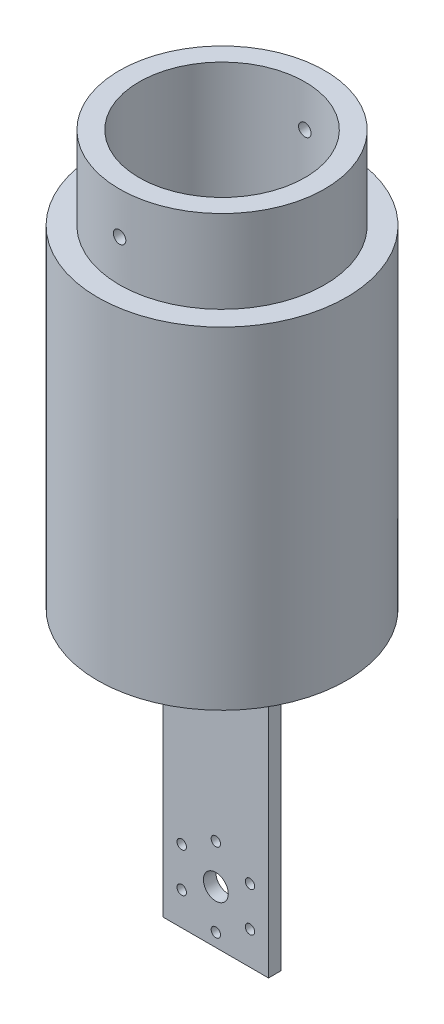
SolidWorks part; units mm, degrees
ref_plane "Front Plane" through (0, 0, 0) normal (0, 0, 1) x (1, 0, 0)
ref_plane "Top Plane" through (0, 0, 0) normal (0, 1, 0) x (1, 0, 0)
ref_plane "Right Plane" through (0, 0, 0) normal (1, 0, 0) x (0, 0, -1)
sketch "Sketch2" plane through (0, 0, 0) normal (0, 1, 0) x (1, 0, 0)
  line L0 (0, 0) -> (25.4, 0)
  line L1 (25.4, 0) -> (25.4, 3)
  line L2 (25.4, 3) -> (0, 3)
  line L3 (0, 3) -> (0, 0)
  dimension "D2" = 3
  dimension "D1" = 25.4
extrude "Boss-Extrude1" add sketch "Sketch2" along normal blind 70
sketch "Sketch3" plane through (0, 0, 0) normal (0, 0, 1) x (1, 0, 0)
  line L0 (0, 0) -> (12.7, 0) construction
  line L1 (0, 0) -> (25.4, 0) construction
  line L2 (12.7, 0) -> (12.7, 12.7) construction
  circle A0 centre (12.7, 12.7) radius 3
  circle A2 centre (12.7, 22.2) radius 1.4
  circle A3 centre (20.9272, 17.45) radius 1.4
  circle A4 centre (20.9272, 7.95) radius 1.4
  circle A5 centre (12.7, 3.2) radius 1.4
  circle A6 centre (4.4728, 7.95) radius 1.4
  circle A7 centre (4.4728, 17.45) radius 1.4
  point P23 (12.7, 12.7)
  dimension "D2" = 6
  dimension "D4" = 2.8
  dimension "D1" = 12.7
  dimension "D5" = 6
sketch "Sketch4" plane through (0, 70, 0) normal (0, 1, 0) x (1, 0, 0)
  circle A0 centre (12.7, 1.5) radius 30
  dimension "D1" = 60
extrude "Boss-Extrude2" add sketch "Sketch4" along normal blind 10
sketch "Sketch5" plane through (0, 80, 0) normal (0, 1, 0) x (1, 0, 0)
  circle A0 centre (12.7, 1.5) radius 30
  circle A1 centre (12.7, 1.5) radius 20
  dimension "D1" = 40
extrude "Boss-Extrude3" add sketch "Sketch5" along normal blind 70
sketch "Sketch8" plane through (0, 150, 0) normal (0, 1, 0) x (1, 0, 0)
  circle A0 centre (12.7, 1.5) radius 24.75
  circle A1 centre (12.7, 1.5) radius 20
  dimension "D1" = 49.5
extrude "Boss-Extrude4" add sketch "Sketch8" along normal blind 20
sketch "Sketch9" plane through (0, 0, 0) normal (0, 0, 1) x (1, 0, 0)
  line L0 (12.7, 170) -> (12.7, 160) construction
  line L1 (37.45, 170) -> (-12.05, 170) construction
  circle A0 centre (12.7, 160) radius 1.5
  dimension "D2" = 3
  dimension "D1" = 10
extrude "Cut-Extrude4" cut sketch "Sketch9" against normal through all and the other way through all
hole_wizard "#4-40 Tapped Hole1" positions "Sketch11" profile "Sketch10" tap size "#4-40" standard "ANSI Inch"
sketch "Sketch11" plane through (0, 0, 0) normal (0, 0, 1) x (1, 0, 0)
  point P0 (12.7, 22.2)
  point P3 (20.9272, 17.45)
  point P6 (20.9272, 7.95)
  point P9 (12.7, 3.2)
  point P12 (4.4728, 7.95)
  point P15 (4.4728, 17.45)
sketch "Sketch10" plane through (12.7, 22.2, 0) normal (1, 0, 0) x (0, -1, 0)
  line L0 (0, 0) -> (0, 8.2792)
  line L1 (0, 8.2792) -> (1.1303, 7.6)
  line L2 (1.1303, 7.6) -> (1.1303, 0)
  line L5 (1.1303, 0) -> (0, 0)
  line L10 (0, 8.2792) -> (-1.1303, 7.6) construction
  line L11 (0, -6.35) -> (0, 107.95) construction
  dimension "Tap Drill Dia." = 2.2606
  dimension "Tap Drill Depth" = 7.6
  dimension "Drill Angle" = 118
cosmetic thread "Hole Thread1"
cosmetic thread "Hole Thread2"
cosmetic thread "Hole Thread3"
cosmetic thread "Hole Thread4"
cosmetic thread "Hole Thread5"
cosmetic thread "Hole Thread6"
extrude "Cut-Extrude5" cut sketch "Sketch3" against normal blind 10 contours A0
